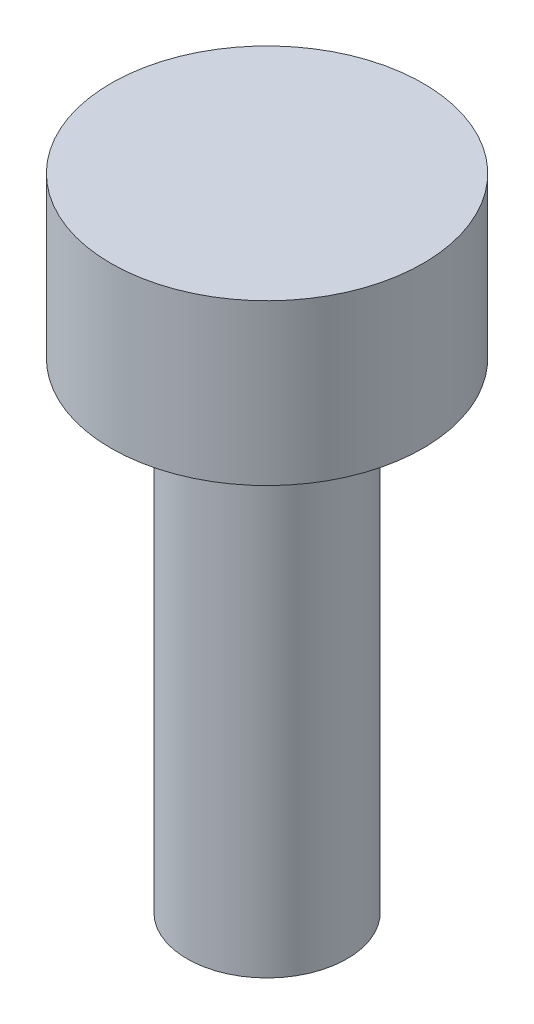
SolidWorks part; units mm, degrees
ref_plane "Front Plane" through (0, 0, 0) normal (0, 0, 1) x (1, 0, 0)
ref_plane "Top Plane" through (0, 0, 0) normal (0, 1, 0) x (1, 0, 0)
ref_plane "Right Plane" through (0, 0, 0) normal (1, 0, 0) x (0, 0, -1)
sketch "Sketch1" plane through (0, 0, 0) normal (0, 1, 0) x (1, 0, 0)
  circle A0 centre (0, 0) radius 1.95
  dimension "D1" = 3.9
extrude "Boss-Extrude1" add sketch "Sketch1" along normal blind 2
sketch "Sketch2" plane through (0, 0, 0) normal (0, -1, 0) x (1, 0, 0)
  circle A0 centre (0, 0) radius 1
  dimension "D1" = 2
extrude "Boss-Extrude2" add sketch "Sketch2" along normal blind 6
